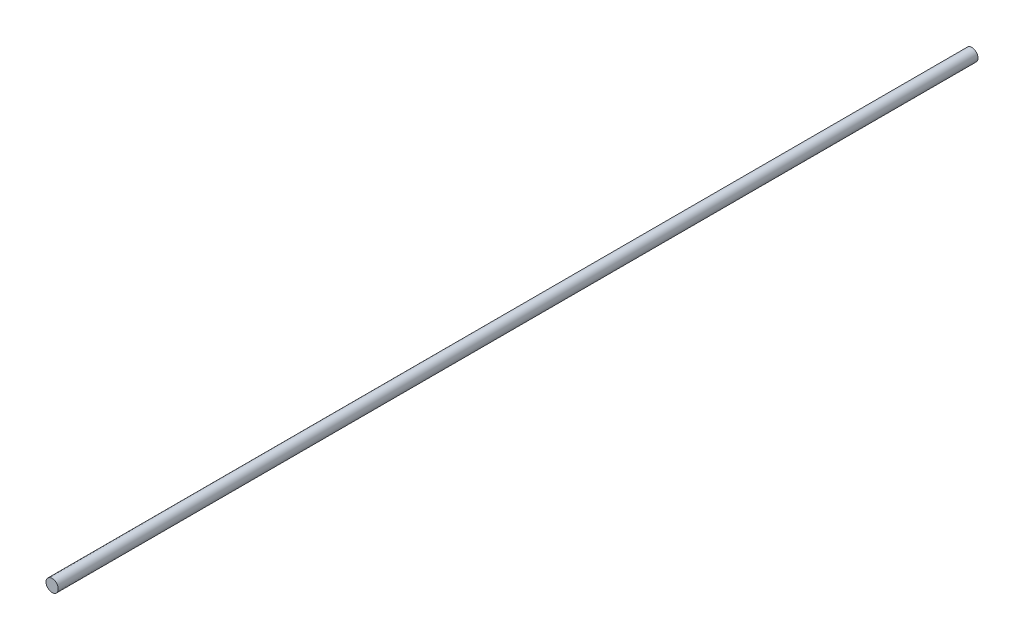
SolidWorks part; units mm, degrees
ref_plane "Plan de face" through (0, 0, 0) normal (0, 0, 1) x (1, 0, 0)
ref_plane "Plan de dessus" through (0, 0, 0) normal (0, 1, 0) x (1, 0, 0)
ref_plane "Plan de droite" through (0, 0, 0) normal (1, 0, 0) x (0, 0, -1)
sketch "Esquisse1" plane through (0, 0, 0) normal (0, 0, 1) x (1, 0, 0)
  circle A0 centre (0, 0) radius 4
  dimension "D1" = 8
extrude "Boss.-Extru.1" add sketch "Esquisse1" along normal blind 600
